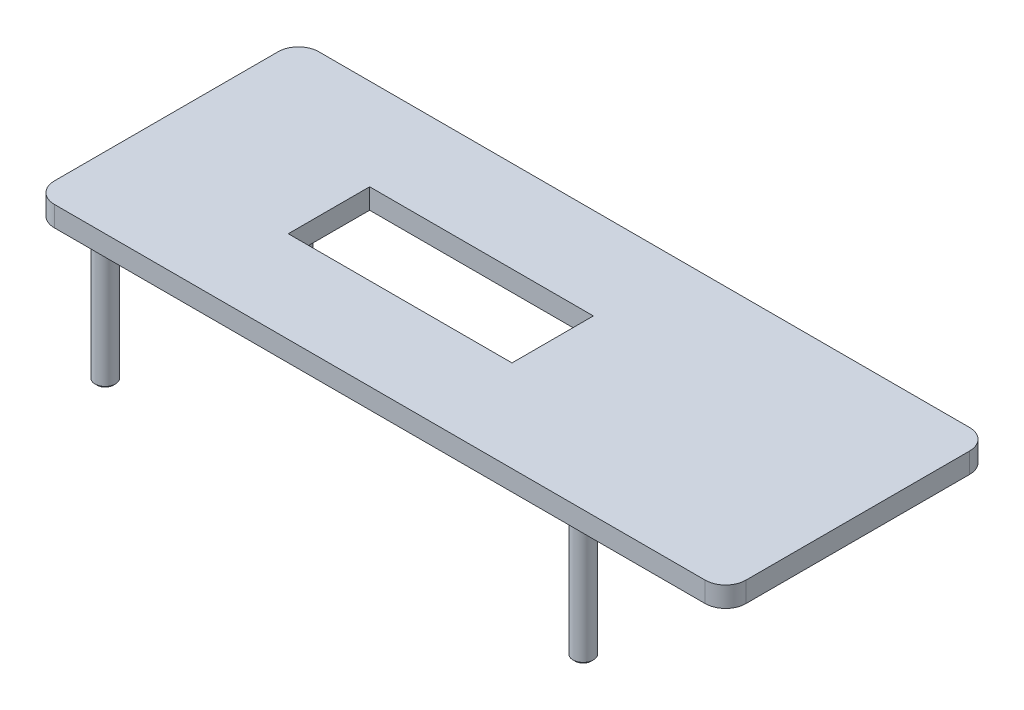
SolidWorks part; units mm, degrees
material "PBT General Purpose"
ref_plane "Front Plane" through (0, 0, 0) normal (0, 0, 1) x (1, 0, 0)
ref_plane "Top Plane" through (0, 0, 0) normal (0, 1, 0) x (1, 0, 0)
ref_plane "Right Plane" through (0, 0, 0) normal (1, 0, 0) x (0, 0, -1)
sketch "Sketch1" plane through (0, 0, 0) normal (0, 1, 0) x (1, 0, 0)
  line L1 (-16, -6.5) -> (16, -6.5)
  line L2 (-17, -5.5) -> (-17, 5.5)
  line L3 (-16, 6.5) -> (16, 6.5)
  line L4 (17, -5.5) -> (17, 5.5)
  line L5 (-17, -6.5) -> (17, 6.5) construction
  line L6 (-17, 6.5) -> (17, -6.5) construction
  arc A0 (16, 6.5) -> (17, 5.5) centre (16, 5.5) cw
  arc A1 (16, -6.5) -> (17, -5.5) centre (16, -5.5) ccw
  arc A2 (-16, -6.5) -> (-17, -5.5) centre (-16, -5.5) cw
  arc A3 (-17, 5.5) -> (-16, 6.5) centre (-16, 5.5) cw
  point P0 (0, 0)
  dimension "D3" = 1
  dimension "D1" = 13
  dimension "D2" = 34
extrude "Boss-Extrude1" add sketch "Sketch1" along normal blind 1
sketch "Sketch2" plane through (0, 0, 0) normal (0, -1, 0) x (1, 0, 0)
  line L0 (-17, -5.5) -> (-17, 5.5) construction
  line L1 (-16, 6.5) -> (16, 6.5) construction
  line L3 (0.55, 0) -> (-0.55, 0) construction
  circle A0 centre (-15.25, 4.75) radius 0.5
  circle A3 centre (-15.25, -4.75) radius 0.5
  circle A4 centre (8.25, -4.75) radius 0.5
  circle A5 centre (8.25, 4.75) radius 0.5
  dimension "D1" = 1
  dimension "D5" = 23.5
  dimension "D2" = 1.75
  dimension "D3" = 1.75
  dimension "D4" = 2
extrude "Boss-Extrude2" add sketch "Sketch2" along normal blind 7
sketch "Sketch4" plane through (0, 1, 0) normal (0, 1, 0) x (1, 0, 0)
  line L0 (-17, 5.5) -> (-17, -5.5) construction
  line L1 (-9, -2) -> (2, -2)
  line L2 (-9, -2) -> (-9, 2)
  line L3 (-9, 2) -> (2, 2)
  line L4 (2, -2) -> (2, 2)
  line L5 (-9, -2) -> (2, 2) construction
  line L6 (-9, 2) -> (2, -2) construction
  point P0 (-3.5, 0)
  point P5 (0, 0)
  dimension "D1" = 8
  dimension "D2" = 4
  dimension "D3" = 11
extrude "Cut-Extrude1" cut sketch "Sketch4" against normal through all both and the other way through all
chamfer "Chamfer2" distance 0.1 angle 45 4 edges at (8.25, -7, -4.25) (8.25, -7, 4.25) (-15.25, -7, -4.25) (-15.25, -7, 4.25)
